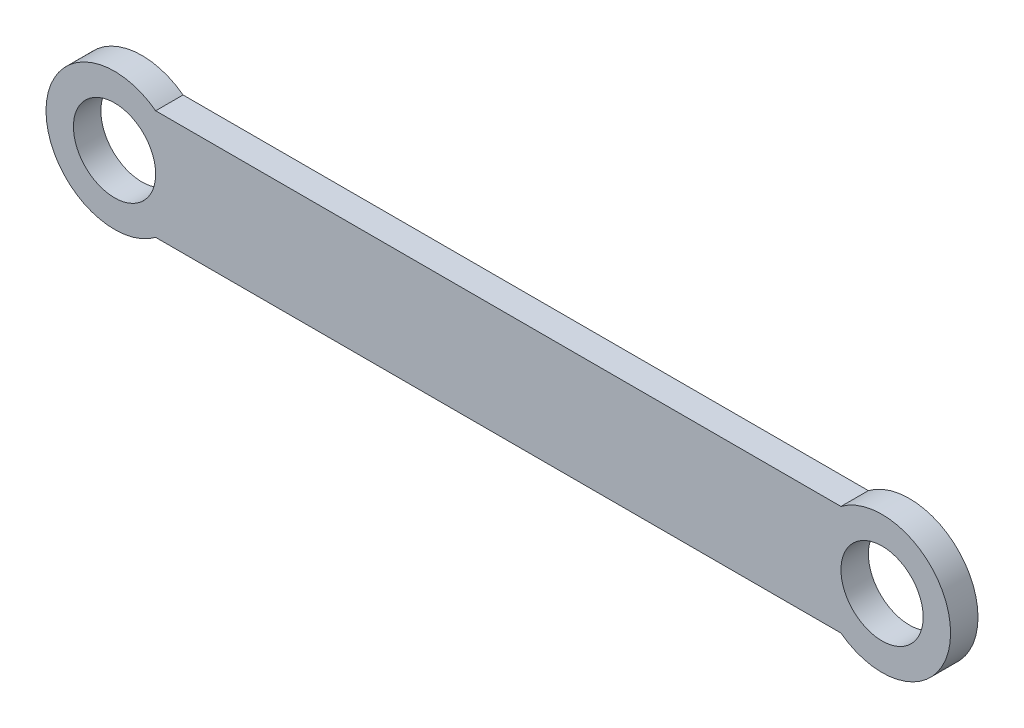
SolidWorks part; units mm, degrees
ref_plane "前视基准面" through (0, 0, 0) normal (0, 0, 1) x (1, 0, 0)
ref_plane "上视基准面" through (0, 0, 0) normal (0, 1, 0) x (1, 0, 0)
ref_plane "右视基准面" through (0, 0, 0) normal (1, 0, 0) x (0, 0, -1)
sketch "草图1" plane through (0, 0, 0) normal (0, 0, 1) x (1, 0, 0)
  line L1 (22.5898, 2.1981) -> (47.5898, 2.1981)
  line L3 (22.5898, -1.8019) -> (47.5898, -1.8019)
  arc A0 (47.5898, -1.8019) -> (47.5898, 2.1981) centre (49.0898, 0.1981) ccw
  arc A1 (22.5898, 2.1981) -> (22.5898, -1.8019) centre (21.0898, 0.1981) ccw
  circle A2 centre (49.0898, 0.1981) radius 1.5
  circle A3 centre (21.0898, 0.1981) radius 1.5
  point P0 (0, 0)
  dimension "D2" = 5
  dimension "D4" = 5
  dimension "D1" = 4
  dimension "D3" = 28
extrude "凸台-拉伸1" add sketch "草图1" along normal blind 1
